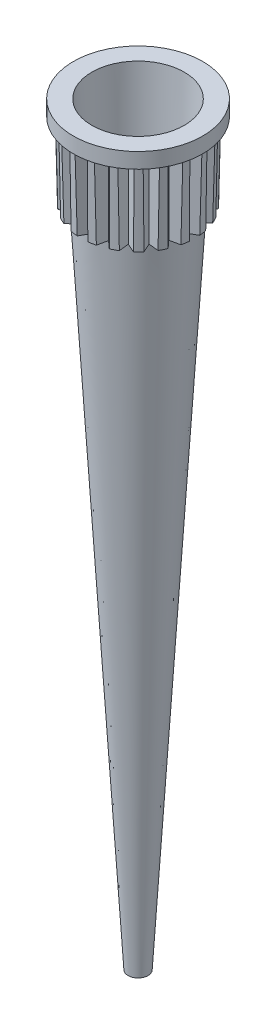
SolidWorks part; units mm, degrees
ref_plane "Ön Düzlem" through (0, 0, 0) normal (0, 0, 1) x (1, 0, 0)
ref_plane "Üst Düzlem" through (0, 0, 0) normal (0, 1, 0) x (1, 0, 0)
ref_plane "Sağ Düzlem" through (0, 0, 0) normal (1, 0, 0) x (0, 0, -1)
sketch "Çizim1" plane through (0, 0, 0) normal (0, 0, 1) x (1, 0, 0)
  line L0 (0, 0) -> (0, 49)
  line L1 (0, 49) -> (4.2, 49)
  line L2 (4.2, 49) -> (4.2, 48)
  line L3 (4.2, 48) -> (3.8, 48)
  line L4 (3.8, 48) -> (3.7, 43)
  line L5 (3.7, 43) -> (3.15, 43)
  line L7 (3.15, 43) -> (0.65, 0)
  line L8 (0.65, 0) -> (0, 0)
  dimension "D1" = 49
  dimension "D2" = 1
  dimension "D3" = 3.8
  dimension "D4" = 5
  dimension "D5" = 3.15
  dimension "D6" = 0.65
  dimension "D7" = 4.2
  dimension "D8" = 3.7
  dimension "D9" = 43
revolve "Döndür1" add sketch "Çizim1" angle 360 about L0
sketch "Çizim2" plane through (0, 49, 0) normal (0, 1, 0) x (1, 0, 0)
  circle A0 centre (0, 0) radius 3
  dimension "D1" = 6
extrude "Kes-Ekstrüzyon1" cut sketch "Çizim2" against normal up to surface (49 mm away) draft 3
sketch "Çizim3" plane through (0, 43, 0) normal (0, -1, 0) x (1, 0, 0)
  line L0 (0.0822, 3.1) -> (-0.4178, 3.966)
  line L1 (-0.4178, 3.966) -> (0.5822, 3.966)
  line L2 (0.5822, 3.966) -> (0.0822, 3.1)
  line L3 (0.8153, 3.9189) -> (1.7663, 3.6099)
  line L4 (1.0232, 2.9408) -> (0.8153, 3.9189)
  line L5 (1.7663, 3.6099) -> (1.0232, 2.9408)
  line L6 (1.9734, 3.4931) -> (2.7824, 2.9053)
  line L7 (1.8688, 2.4985) -> (1.9734, 3.4931)
  line L8 (2.7824, 2.9053) -> (1.8688, 2.4985)
  line L9 (2.9432, 2.7302) -> (3.531, 1.9212)
  line L10 (2.5365, 1.8167) -> (2.9432, 2.7302)
  line L11 (3.531, 1.9212) -> (2.5365, 1.8167)
  line L12 (3.6298, 1.705) -> (3.9388, 0.7539)
  line L13 (2.9607, 0.9618) -> (3.6298, 1.705)
  line L14 (3.9388, 0.7539) -> (2.9607, 0.9618)
  line L15 (3.966, 0.5178) -> (3.966, -0.4822)
  line L16 (3.1, 0.0178) -> (3.966, 0.5178)
  line L17 (3.966, -0.4822) -> (3.1, 0.0178)
  line L18 (3.9189, -0.7153) -> (3.6099, -1.6663)
  line L19 (2.9408, -0.9232) -> (3.9189, -0.7153)
  line L20 (3.6099, -1.6663) -> (2.9408, -0.9232)
  line L21 (3.4931, -1.8734) -> (2.9053, -2.6824)
  line L22 (2.4985, -1.7688) -> (3.4931, -1.8734)
  line L23 (2.9053, -2.6824) -> (2.4985, -1.7688)
  line L24 (2.7302, -2.8432) -> (1.9212, -3.431)
  line L25 (1.8167, -2.4365) -> (2.7302, -2.8432)
  line L26 (1.9212, -3.431) -> (1.8167, -2.4365)
  line L27 (1.705, -3.5298) -> (0.7539, -3.8388)
  line L28 (0.9618, -2.8607) -> (1.705, -3.5298)
  line L29 (0.7539, -3.8388) -> (0.9618, -2.8607)
  line L30 (0.5178, -3.866) -> (-0.4822, -3.866)
  line L31 (0.0178, -3) -> (0.5178, -3.866)
  line L32 (-0.4822, -3.866) -> (0.0178, -3)
  line L33 (-0.7153, -3.8189) -> (-1.6663, -3.5099)
  line L34 (-0.9232, -2.8408) -> (-0.7153, -3.8189)
  line L35 (-1.6663, -3.5099) -> (-0.9232, -2.8408)
  line L36 (-1.8734, -3.3931) -> (-2.6824, -2.8053)
  line L37 (-1.7688, -2.3985) -> (-1.8734, -3.3931)
  line L38 (-2.6824, -2.8053) -> (-1.7688, -2.3985)
  line L39 (-2.8432, -2.6302) -> (-3.431, -1.8212)
  line L40 (-2.4365, -1.7167) -> (-2.8432, -2.6302)
  line L41 (-3.431, -1.8212) -> (-2.4365, -1.7167)
  line L42 (-3.5298, -1.605) -> (-3.8388, -0.6539)
  line L43 (-2.8607, -0.8618) -> (-3.5298, -1.605)
  line L44 (-3.8388, -0.6539) -> (-2.8607, -0.8618)
  line L45 (-3.866, -0.4178) -> (-3.866, 0.5822)
  line L46 (-3, 0.0822) -> (-3.866, -0.4178)
  line L47 (-3.866, 0.5822) -> (-3, 0.0822)
  line L48 (-3.8189, 0.8153) -> (-3.5099, 1.7663)
  line L49 (-2.8408, 1.0232) -> (-3.8189, 0.8153)
  line L50 (-3.5099, 1.7663) -> (-2.8408, 1.0232)
  line L51 (-3.3931, 1.9734) -> (-2.8053, 2.7824)
  line L52 (-2.3985, 1.8688) -> (-3.3931, 1.9734)
  line L53 (-2.8053, 2.7824) -> (-2.3985, 1.8688)
  line L54 (-2.6302, 2.9432) -> (-1.8212, 3.531)
  line L55 (-1.7167, 2.5365) -> (-2.6302, 2.9432)
  line L56 (-1.8212, 3.531) -> (-1.7167, 2.5365)
  line L57 (-1.605, 3.6298) -> (-0.6539, 3.9388)
  line L58 (-0.8618, 2.9607) -> (-1.605, 3.6298)
  line L59 (-0.6539, 3.9388) -> (-0.8618, 2.9607)
  point P63 (0.05, 0.05)
  dimension "D1" = 60
  dimension "D2" = 60
  dimension "D3" = 1
  dimension "D4" = 3.1
extrude "Kes-Ekstrüzyon4" cut sketch "Çizim3" against normal blind 5
scale "Scale1" bodies to scale 105 scale about centroid uniform scaling yes scale factor 0.880952
